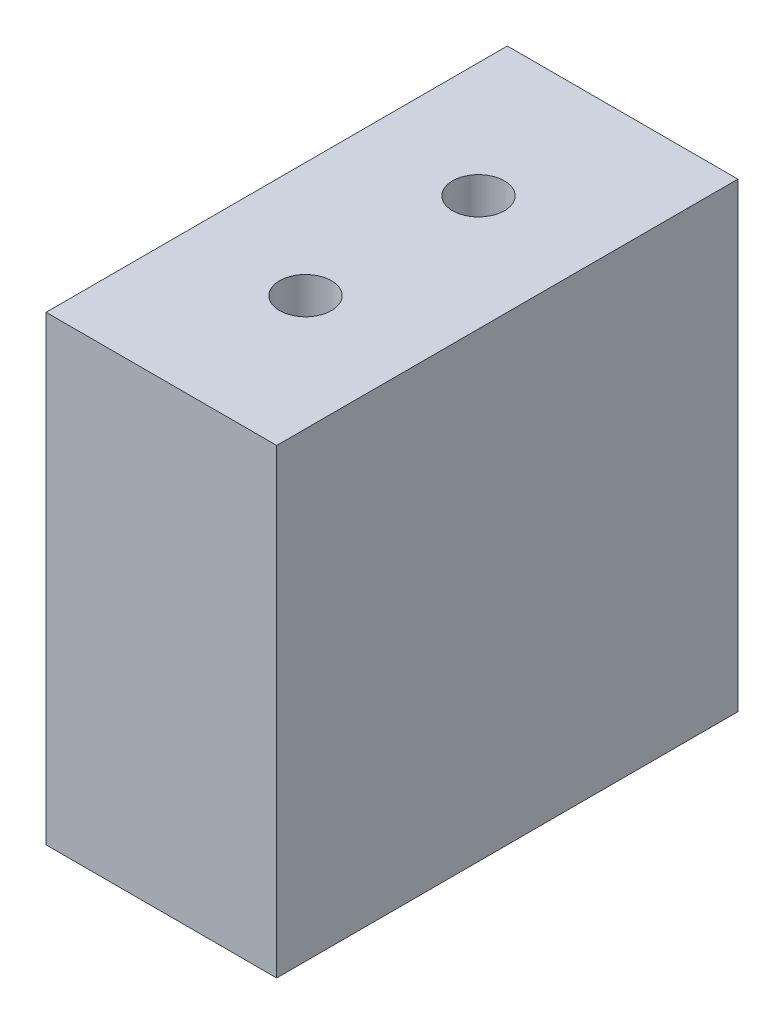
SolidWorks part; units mm, degrees
ref_plane "前视基准面" through (0, 0, 0) normal (0, 0, 1) x (1, 0, 0)
ref_plane "上视基准面" through (0, 0, 0) normal (0, 1, 0) x (1, 0, 0)
ref_plane "右视基准面" through (0, 0, 0) normal (1, 0, 0) x (0, 0, -1)
other "Configuration Table"
sketch "草图1" plane through (0, 0, 0) normal (1, 0, 0) x (0, 0, -1)
  line L1 (0, 0) -> (40, 0)
  line L2 (0, 0) -> (0, 40)
  line L3 (0, 40) -> (40, 40)
  line L4 (40, 0) -> (40, 40)
  dimension "D1" = 40
  dimension "D2" = 40
extrude "凸台-拉伸1" add sketch "草图1" along normal blind 20 contours L3 L4 L1 L2
sketch "草图2" plane through (0, 40, 0) normal (0, 1, 0) x (1, 0, 0)
  line L0 (20, 40) -> (0, 40) construction
  line L1 (20, 0) -> (20, 40) construction
  circle A0 centre (10, 27.5) radius 2.25
  circle A1 centre (10, 12.5) radius 2.25
  dimension "D1" = 12.5
  dimension "D2" = 10
  dimension "D3" = 4.5
  dimension "D4" = 15
  dimension "D5" = 4.5
  dimension "D6" = 10
extrude "切除-拉伸1" cut sketch "草图2" against normal through all
